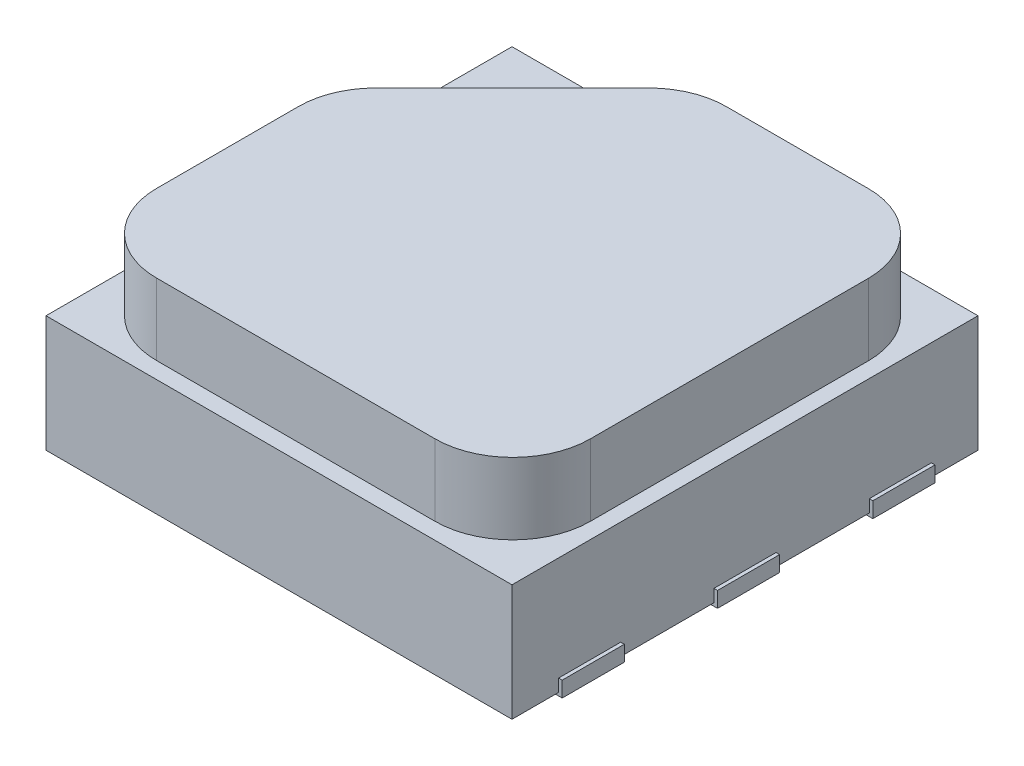
SolidWorks part; units mm, degrees
ref_plane "Front Plane" through (0, 0, 0) normal (0, 0, 1) x (1, 0, 0)
ref_plane "Top Plane" through (0, 0, 0) normal (0, 1, 0) x (1, 0, 0)
ref_plane "Right Plane" through (0, 0, 0) normal (1, 0, 0) x (0, 0, -1)
sketch "Sketch1" plane through (0, 0, 0) normal (0, 1, 0) x (1, 0, 0)
  line L1 (0, 0) -> (3, 0)
  line L2 (0, 0) -> (0, 3)
  line L3 (0, 3) -> (3, 3)
  line L4 (3, 0) -> (3, 3)
  dimension "D1" = 3
  dimension "D2" = 3
extrude "Boss-Extrude1" add sketch "Sketch1" along normal blind 0.75
ref_plane "Plane1" through (0, 0.75, 0) normal (0, 1, 0) x (1, 0, 0)
sketch "Sketch2" plane through (0, 0.75, 0) normal (0, 1, 0) x (1, 0, 0)
  line L9 (0.1061, 0.1061) -> (2.8986, 0.1061)
  line L10 (0.1061, 0.1061) -> (0.1061, 2.896)
  line L11 (0.1061, 2.896) -> (2.8986, 2.896)
  line L12 (2.8986, 0.1061) -> (2.8986, 2.896)
extrude "Boss-Extrude2" add sketch "Sketch2" along normal blind 0.46
fillet "Fillet1" radius 0.5 3 edges at (2.8986, 0.98, -2.896) (2.8986, 0.98, -0.1061) (0.1061, 0.98, -0.1061)
chamfer "Chamfer1" distance 1.17 angle 45 1 edges at (0.1061, 0.98, -2.896)
fillet "Fillet2" radius 0.5 2 edges at (0.1061, 0.98, -1.726) (1.2761, 0.98, -2.896)
ref_plane "Plane3" through (0, 0, 0) normal (0, -1, 0) x (-1, 0, 0)
sketch "Sketch4" plane through (0, 0, 0) normal (0, -1, 0) x (-1, 0, 0)
  line L0 (-0.2, 0.3) -> (0, 0.3)
  line L1 (0, 3) -> (0, 0) construction
  line L2 (-0.2, 0.7) -> (0, 0.7)
  line L3 (0, 0.3) -> (0.0231, 0.3)
  line L4 (-0.2, 1.3) -> (0, 1.3)
  line L5 (0, 1.3) -> (0.0231, 1.3)
  line L6 (-0.2, 2.7) -> (0, 2.7)
  line L7 (-0.2, 1.7) -> (0, 1.7)
  line L8 (-0.2, 2.3001) -> (0, 2.3001)
  line L9 (0, 2.7) -> (0.0231, 2.7)
  line L10 (0.0231, 0.3) -> (0.0231, 0.7)
  line L11 (0.0231, 0.7) -> (0, 0.7)
  line L12 (0.0231, 1.3) -> (0.0231, 1.7)
  line L13 (0.0231, 1.7) -> (0, 1.7)
  line L14 (0.0231, 2.7) -> (0.0231, 2.3001)
  line L15 (0.0231, 2.3001) -> (0, 2.3001)
  arc A0 (-0.2, 1.3) -> (-0.2, 1.7) centre (-0.2, 1.5) cw
  arc A1 (-0.2, 0.3) -> (-0.2, 0.7) centre (-0.2, 0.5) cw
  arc A2 (-0.2, 2.3001) -> (-0.2, 2.7) centre (-0.2, 2.5) cw
extrude "Boss-Extrude3" add sketch "Sketch4" against normal blind 0.1 from offset 0.02
ref_plane "Plane4" through (1.5, 0, 0) normal (1, 0, 0) x (0, 0, -1)
mirror "Mirror1" about plane through (1.5, 0, 0) normal (1, 0, 0) of "Boss-Extrude3"
